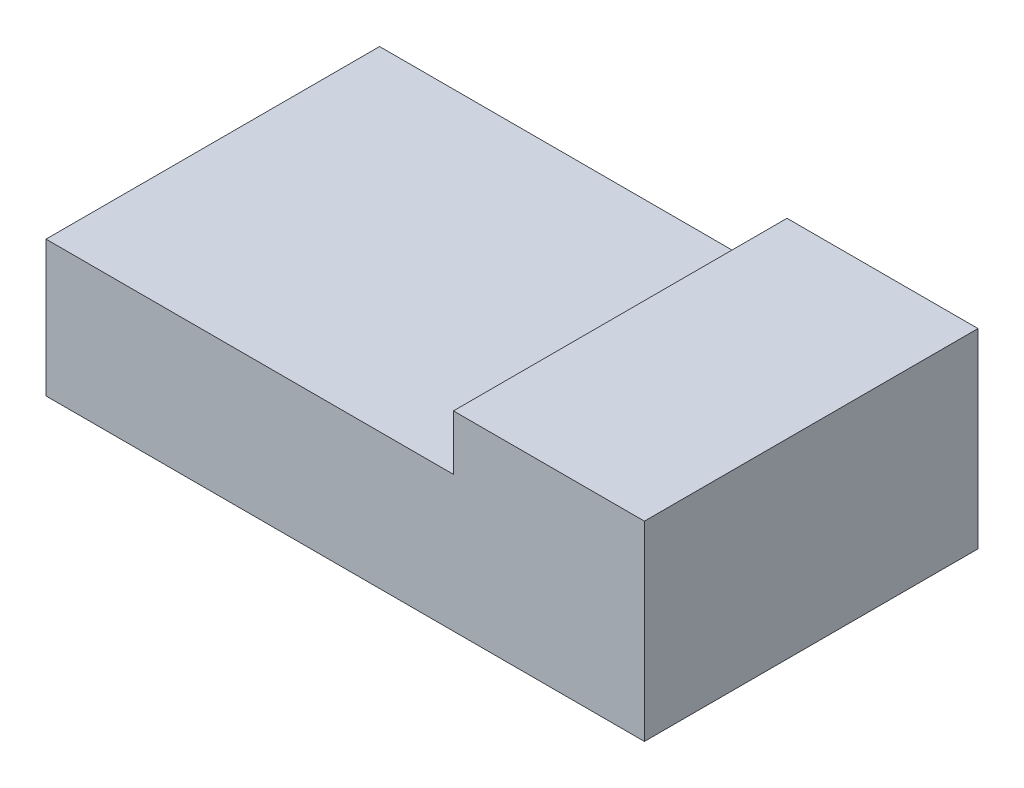
SolidWorks part; units mm, degrees
ref_plane "Front Plane" through (0, 0, 0) normal (0, 0, 1) x (1, 0, 0)
ref_plane "Top Plane" through (0, 0, 0) normal (0, 1, 0) x (1, 0, 0)
ref_plane "Right Plane" through (0, 0, 0) normal (1, 0, 0) x (0, 0, -1)
sketch "Sketch1" plane through (0, 0, 0) normal (0, 1, 0) x (1, 0, 0)
  line L1 (0, 0) -> (47, 0)
  line L2 (0, 0) -> (0, -26.2)
  line L3 (0, -26.2) -> (47, -26.2)
  line L4 (47, 0) -> (47, -26.2)
  dimension "D1" = 47
  dimension "D2" = 26.2
extrude "Boss-Extrude1" add sketch "Sketch1" along normal blind 10.668
sketch "Sketch2" plane through (0, 10.668, 0) normal (0, 1, 0) x (1, 0, 0)
  line L0 (0, -26.2) -> (47, -26.2) construction
  line L1 (47, 0) -> (32, 0)
  line L2 (47, 0) -> (47, -26.2)
  line L3 (47, -26.2) -> (32, -26.2)
  line L4 (32, 0) -> (32, -26.2)
  dimension "D1" = 15
extrude "Boss-Extrude2" add sketch "Sketch2" along normal offset from surface (4.318 mm away) 14.986 up to face at (23.5, 0, 13.1)
